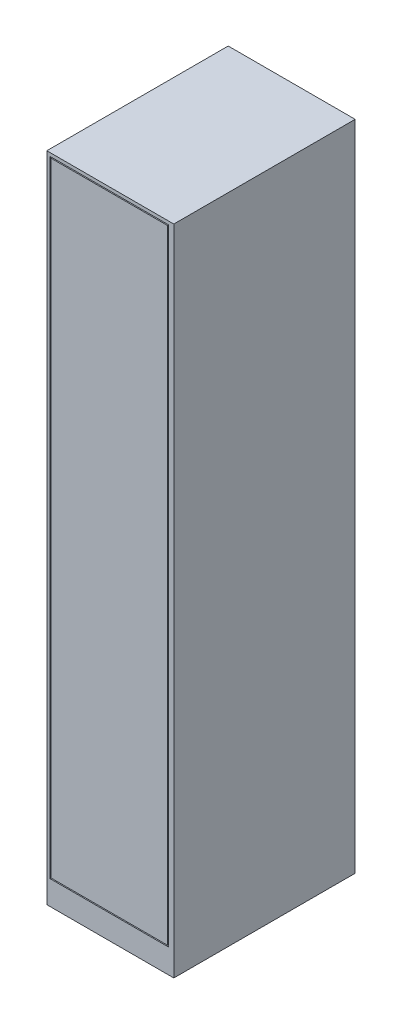
SolidWorks part; units mm, degrees
ref_plane "Front Plane" through (0, 0, 0) normal (0, 0, 1) x (1, 0, 0)
ref_plane "Top Plane" through (0, 0, 0) normal (0, 1, 0) x (1, 0, 0)
ref_plane "Right Plane" through (0, 0, 0) normal (1, 0, 0) x (0, 0, -1)
sketch "Sketch1" plane through (0, 0, 0) normal (0, 0, 1) x (1, 0, 0)
  line L1 (0, 0) -> (350, 0)
  line L2 (0, 0) -> (0, 1800)
  line L3 (0, 1800) -> (350, 1800)
  line L4 (350, 0) -> (350, 1800)
extrude "Boss-Extrude1" add sketch "Sketch1" along normal blind 500
ref_plane "Plane1" through (0, 0, 500) normal (0, 0, 1) x (1, 0, 0)
sketch "Sketch2" plane through (0, 0, 500) normal (0, 0, 1) x (1, 0, 0)
  line L1 (8.829, 1790.851) -> (335.9247, 1790.851)
  line L2 (8.829, 1790.851) -> (8.829, 66.6139)
  line L3 (8.829, 66.6139) -> (335.9247, 66.6139)
  line L4 (335.9247, 1790.851) -> (335.9247, 66.6139)
extrude "Cut-Extrude-Thin1" cut sketch "Sketch2" against normal blind 3 thin
